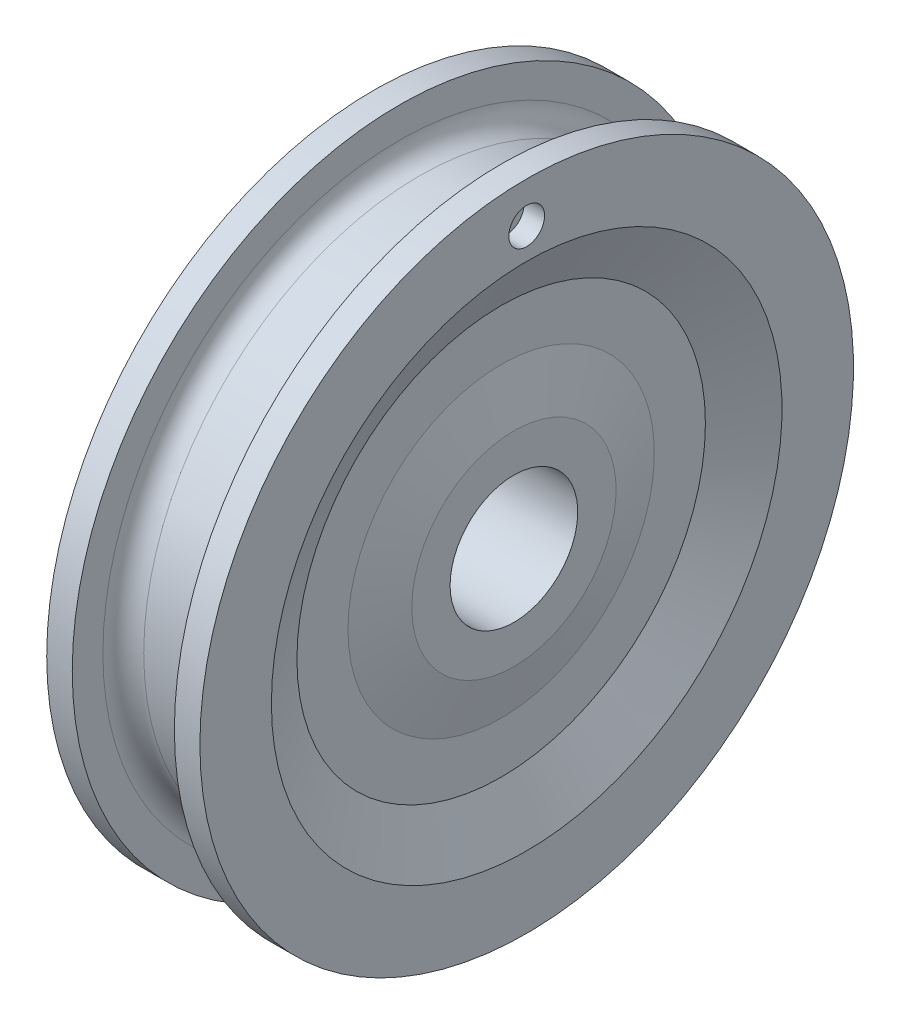
SolidWorks part; units mm, degrees
ref_plane "Plano frontal" through (0, 0, 0) normal (0, 0, 1) x (1, 0, 0)
ref_plane "Plano superior" through (0, 0, 0) normal (0, 1, 0) x (1, 0, 0)
ref_plane "Plano direito" through (0, 0, 0) normal (1, 0, 0) x (0, 0, -1)
sketch "Esboço2" plane through (0, 0, 0) normal (0, 0, 1) x (1, 0, 0)
  line L0 (0, 0) -> (20.3488, 0) construction
  line L1 (1.25, 6.25) -> (13.75, 6.25)
  line L2 (13.75, 6.25) -> (13.75, 10)
  line L3 (13.75, 10) -> (12.5, 15)
  line L4 (12.5, 15) -> (12.5, 20)
  line L5 (12.5, 20) -> (15, 25)
  line L6 (15, 25) -> (15, 32)
  line L7 (15, 32) -> (12.5, 32)
  line L8 (12.5, 32) -> (12.5, 29)
  line L9 (10.5, 27) -> (4.5, 27)
  line L10 (2.5, 29) -> (2.5, 32)
  line L11 (2.5, 32) -> (0, 32)
  line L12 (0, 32) -> (0, 25)
  line L13 (0, 25) -> (2.5, 20)
  line L14 (2.5, 20) -> (2.5, 15)
  line L15 (2.5, 15) -> (1.25, 10)
  line L16 (1.25, 10) -> (1.25, 6.25)
  arc A8 (12.5, 29) -> (10.5, 27) centre (10.5, 29) cw
  arc A9 (4.5, 27) -> (2.5, 29) centre (4.5, 29) cw
  dimension "D12" = 50
  dimension "D7" = 2
  dimension "D1" = 12.5
  dimension "D2" = 64
  dimension "D3" = 54
  dimension "D4" = 15
  dimension "D5" = 10
  dimension "D6" = 12.5
  dimension "D8" = 20
  dimension "D9" = 10
  dimension "D10" = 30
  dimension "D11" = 40
revolve "Revolução1" add sketch "Esboço2" angle 360 about L0
sketch "Esboço4" plane through (15, 0, 0) normal (1, 0, 0) x (0, 0, -1)
  line L0 (0, 0) -> (0, 28) construction
  circle A0 centre (0, 28) radius 1.75
  dimension "D1" = 3.5
  dimension "D2" = 28
extrude "Corte-extrusão1" cut sketch "Esboço4" against normal blind 2
